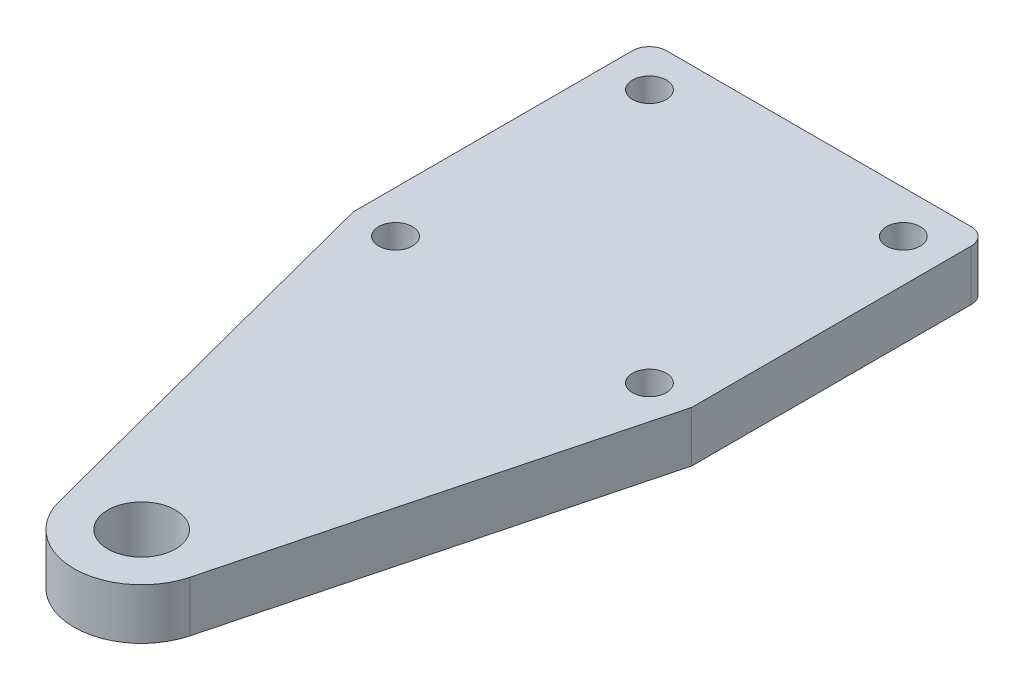
SolidWorks part; units mm, degrees
material "Acrílico (Impacto medio-alto)"
ref_plane "Alzado" through (0, 0, 0) normal (0, 0, 1) x (1, 0, 0)
ref_plane "Planta" through (0, 0, 0) normal (0, 1, 0) x (1, 0, 0)
ref_plane "Vista lateral" through (0, 0, 0) normal (1, 0, 0) x (0, 0, -1)
sketch "Croquis1" plane through (0, 0, 0) normal (0, 1, 0) x (1, 0, 0)
  line L0 (0, 0) -> (7.5, 0) construction
  line L1 (7.5, 0) -> (7.5, 7.5) construction
  line L2 (7.5, 7.5) -> (-7.5, 7.5) construction
  line L3 (-7.5, 7.5) -> (-7.5, -7.5) construction
  line L4 (-7.5, -7.5) -> (7.5, -7.5) construction
  line L5 (7.5, -7.5) -> (7.5, 0) construction
  line L6 (8.5, 7.5) -> (10, 7.5) construction
  line L7 (-7.5, 8.5) -> (-7.5, 10) construction
  line L8 (-8.5, 7.5) -> (-10, 7.5) construction
  line L9 (-8.5, -7.5) -> (-10, -7.5) construction
  line L10 (-10, -7.5) -> (-10, 9)
  line L11 (-9, 10) -> (9, 10)
  line L12 (10, 9) -> (10, -7.5)
  line L13 (0, 0) -> (0, -30) construction
  line L14 (-10, -7.5) -> (-3.8706, -31.0092)
  line L15 (10, -7.5) -> (3.8706, -31.0092)
  circle A0 centre (-7.5, 7.5) radius 1
  circle A1 centre (7.5, 7.5) radius 1
  circle A2 centre (7.5, -7.5) radius 1
  circle A3 centre (-7.5, -7.5) radius 1
  arc A4 (-10, 9) -> (-9, 10) centre (-9, 9) cw
  arc A5 (9, 10) -> (10, 9) centre (9, 9) cw
  circle A6 centre (0, -30) radius 2
  arc A7 (-3.8706, -31.0092) -> (3.8706, -31.0092) centre (0, -30) ccw
  dimension "D1" = 1
  dimension "D2" = 1
extrude "Saliente-Extruir1" add sketch "Croquis1" along normal blind 3
